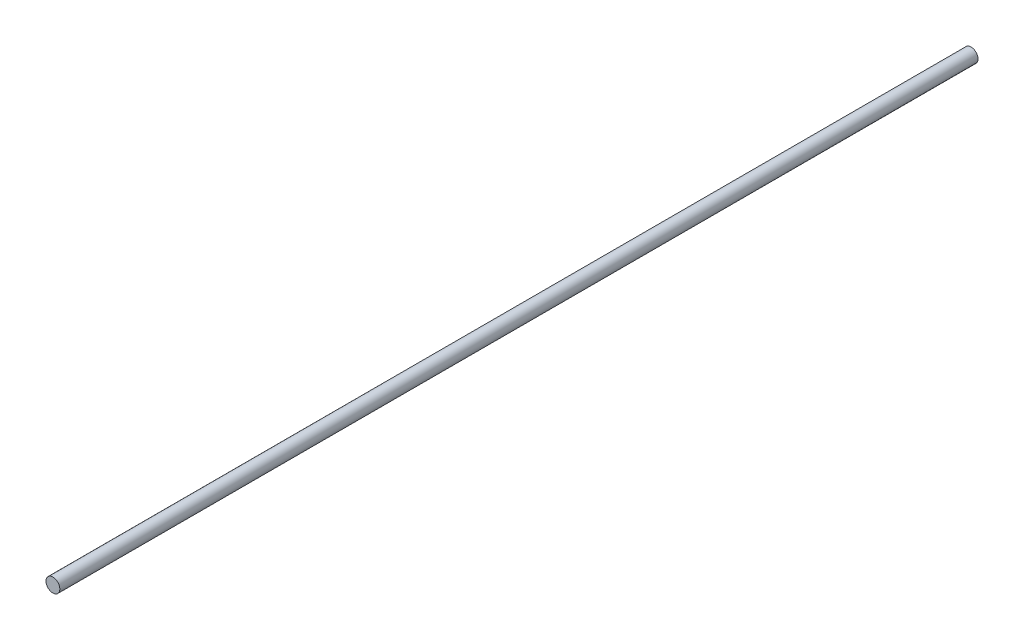
SolidWorks part; units mm, degrees
ref_plane "Front Plane" through (0, 0, 0) normal (0, 0, 1) x (1, 0, 0)
ref_plane "Top Plane" through (0, 0, 0) normal (0, 1, 0) x (1, 0, 0)
ref_plane "Right Plane" through (0, 0, 0) normal (1, 0, 0) x (0, 0, -1)
sketch "Sketch1" plane through (0, 0, 0) normal (0, 0, 1) x (1, 0, 0)
  circle A0 centre (0, 0) radius 3.9688
  dimension "D1" = 7.9375
extrude "Boss-Extrude1" add sketch "Sketch1" along normal mid plane 527.05
